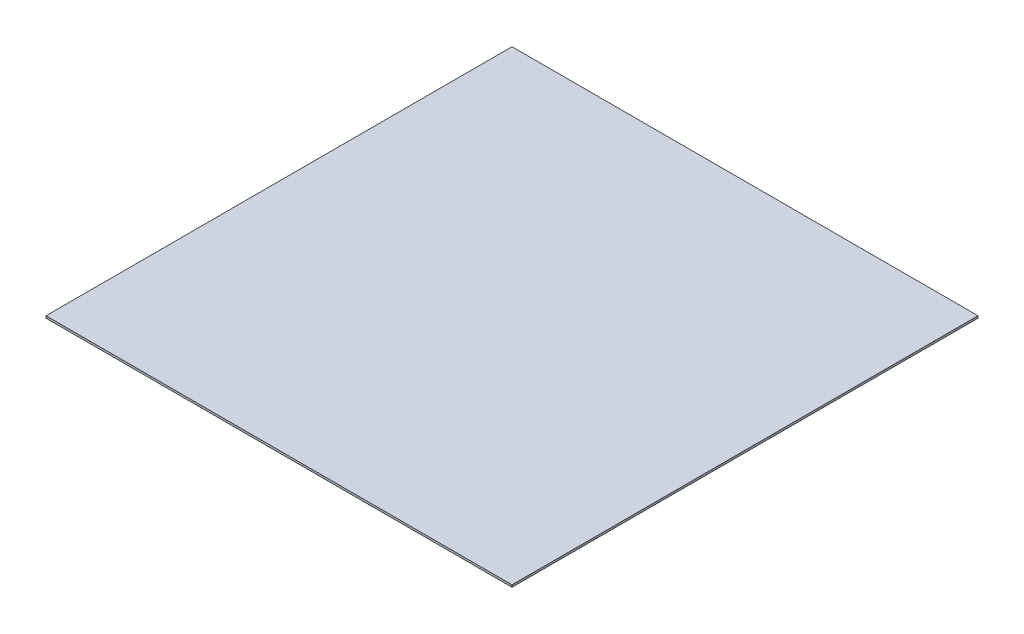
SolidWorks part; units mm, degrees
ref_plane "Front Plane" through (0, 0, 0) normal (0, 0, 1) x (1, 0, 0)
ref_plane "Top Plane" through (0, 0, 0) normal (0, 1, 0) x (1, 0, 0)
ref_plane "Right Plane" through (0, 0, 0) normal (1, 0, 0) x (0, 0, -1)
sketch "Sketch1" plane through (0, 0, 0) normal (0, 1, 0) x (1, 0, 0)
  line L1 (0, 0) -> (558.8, 0)
  line L2 (0, 0) -> (0, -558.8)
  line L3 (0, -558.8) -> (558.8, -558.8)
  line L4 (558.8, 0) -> (558.8, -558.8)
extrude "Boss-Extrude1" add sketch "Sketch1" along normal blind 2.54
